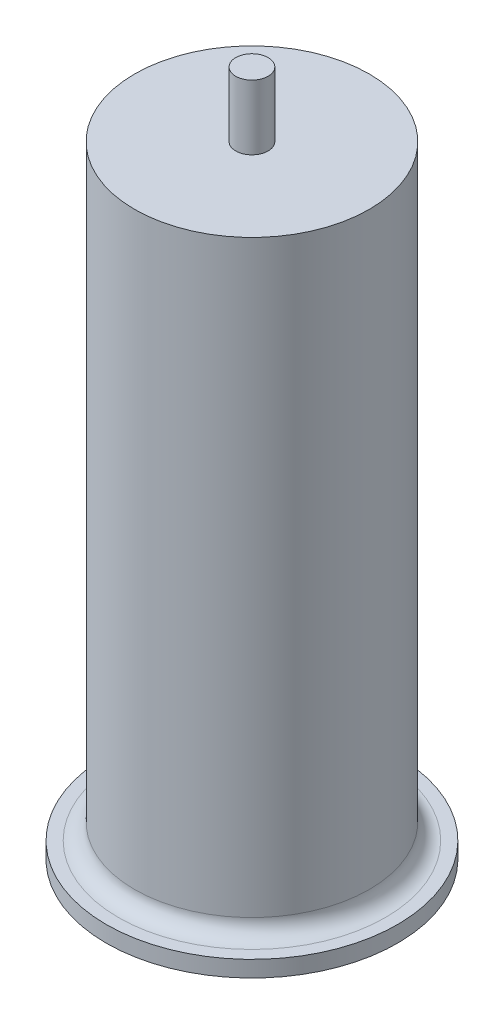
SolidWorks part; units mm, degrees
ref_plane "Front Plane" through (0, 0, 0) normal (0, 0, 1) x (1, 0, 0)
ref_plane "Top Plane" through (0, 0, 0) normal (0, 1, 0) x (1, 0, 0)
ref_plane "Right Plane" through (0, 0, 0) normal (1, 0, 0) x (0, 0, -1)
sketch "Sketch1" plane through (0, 0, 0) normal (0, 1, 0) x (1, 0, 0)
  circle A0 centre (0, 0) radius 72.5
  dimension "D1" = 145
extrude "Boss-Extrude1" add sketch "Sketch1" along normal blind 384 contours A0
sketch "Sketch2" plane through (0, 0, 0) normal (0, 1, 0) x (1, 0, 0)
  circle A0 centre (0, 0) radius 90
  dimension "D1" = 180
extrude "Boss-Extrude2" add sketch "Sketch2" along normal blind 10
fillet "Fillet1" radius 10 1 edges at (0, 10, 72.5)
sketch "Sketch3" plane through (0, 384, 0) normal (0, 1, 0) x (1, 0, 0)
  circle A0 centre (0, 0) radius 10
  dimension "D1" = 20
extrude "Boss-Extrude3" add sketch "Sketch3" along normal blind 40
